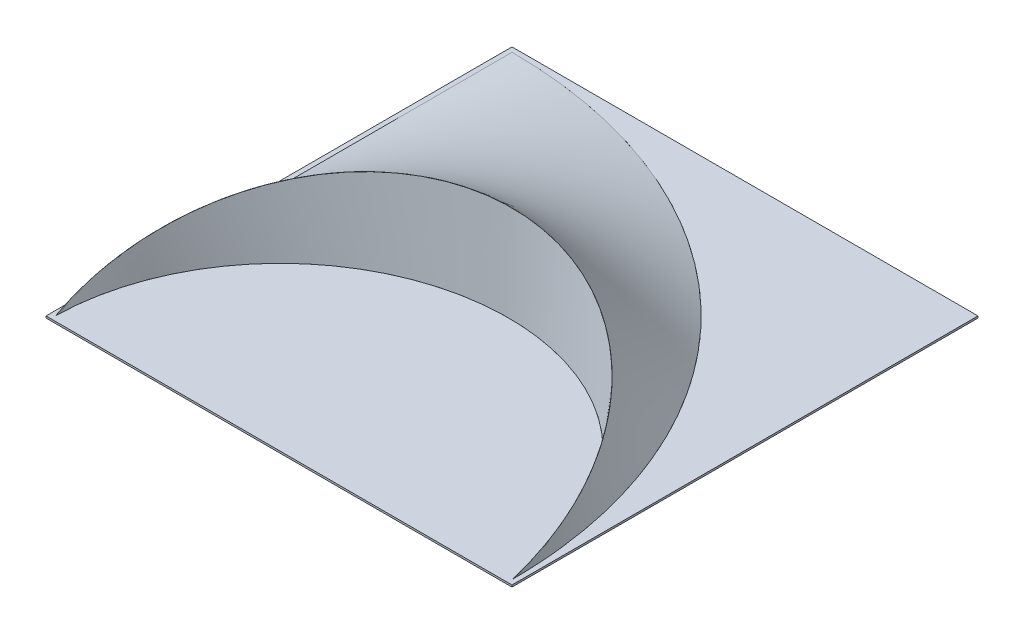
SolidWorks part; units mm, degrees
material "1060 Legierung"
ref_plane "Ebene vorne" through (0, 0, 0) normal (0, 0, 1) x (1, 0, 0)
ref_plane "Ebene oben" through (0, 0, 0) normal (0, 1, 0) x (1, 0, 0)
ref_plane "Ebene rechts" through (0, 0, 0) normal (1, 0, 0) x (0, 0, -1)
sketch "Skizze1" plane through (0, 0, 0) normal (0, 1, 0) x (1, 0, 0)
  line L0 (-244, 244) -> (244, 244) construction
  line L1 (-249, 249) -> (249, 249)
  line L2 (-249, 249) -> (-249, -249)
  line L3 (-249, -249) -> (249, -249)
  line L4 (249, 249) -> (249, -249)
  line L5 (-249, 249) -> (249, -249) construction
  line L6 (-249, -249) -> (249, 249) construction
  line L7 (244, 244) -> (244, -244) construction
  line L8 (-244, -244) -> (244, -244) construction
  line L9 (-244, 244) -> (-244, -244) construction
  line L10 (0, 249) -> (0, -249) construction
  arc A0 (-244, 244) -> (244, -244) centre (-244, -244) cw construction
  arc A1 (-244, -244) -> (244, -244) centre (0, -244) cw construction
  point P0 (0, 0)
  dimension "D1" = 498
  dimension "D2" = 498
  dimension "D3" = 5
extrude "Aufsatz-Linear austragen1" add sketch "Skizze1" against normal blind 2 contours L2 L3 L4 L1
sketch3d "3D-Skizze1"
  line L0 (0, 0, 0) -> (0, 100, 0) construction
  line L2 (0, 100, 0) -> (0, 0, 5.2408) construction
  line L8 (-244, 0, 244) -> (-244, 0, -244)
  line L16 (0, 0, -249) -> (0, 0, 249) construction
  arc A0 (-244, 0, 244) -> (244, 0, 244) centre (0, 7.1905, 226.4551) cw
  arc A1 (244, 0, 244) -> (-244, 0, -244) centre (-244, 0, 244) cw
  arc A4 (-244, 0, 244) -> (244, 0, 244) centre (0, 0, 247.6965) cw construction
  point P5 (0, -219.2646, 133.6457)
  point P10 (-244, 488, 244)
  point P20 (0, -244.028, 247.6965)
  dimension "D1" = 100
  dimension "D2" = 3
surface "Oberflächenausfüllung1" sketch "3D-Skizze1"
sketch3d "3D-Skizze2"
  arc A0 (-244, 0, 244) -> (244, 0, 244) centre (0, 0, 247.6965) cw
  arc A1 (-244, 0, 244) -> (244, 0, 244) centre (0, 7.1729, 226.4959) cw
  spline S0 degree 3 poles (-243.9999, 0, 244) (-244.0404, 0.1982, 243.5162) (-244.1182, 0.5947, 242.5487) (-244.2151, 1.1344, 241.2318) (-244.3084, 1.7019, 239.8471) (-244.3925, 2.2695, 238.4622) (-244.4675, 2.8372, 237.0771) (-244.5334, 3.405, 235.6917) (-244.59, 3.9728, 234.3063) (-244.6375, 4.5407, 232.9207) (-244.6758, 5.1086, 231.535) (-244.7049, 5.6766, 230.1493) (-244.7247, 6.2445, 228.7636) (-244.7354, 6.8124, 227.378) (-244.7369, 7.3802, 225.9924) (-244.7292, 7.948, 224.6069) (-244.7123, 8.5158, 223.2215) (-244.6863, 9.0834, 221.8363) (-244.6511, 9.651, 220.4513) (-244.6067, 10.2185, 219.0666) (-244.5532, 10.7859, 217.6821) (-244.4906, 11.3531, 216.298) (-244.4189, 11.9202, 214.9142) (-244.338, 12.4872, 213.5309) (-244.2481, 13.054, 212.1479) (-244.149, 13.6206, 210.7655) (-244.0408, 14.187, 209.3835) (-243.9234, 14.7531, 208.0021) (-243.7969, 15.3191, 206.6213) (-243.6612, 15.8847, 205.2411) (-243.5163, 16.4501, 203.8616) (-243.3622, 17.0151, 202.4829) (-243.199, 17.5799, 201.1048) (-243.0267, 18.1443, 199.7276) (-242.8452, 18.7084, 198.3512) (-242.6546, 19.2721, 196.9757) (-242.4549, 19.8355, 195.6011) (-242.2461, 20.3985, 194.2275) (-242.0281, 20.961, 192.8548) (-241.801, 21.5231, 191.4832) (-241.5649, 22.0848, 190.1127) (-241.3196, 22.646, 188.7434) (-241.0652, 23.2068, 187.3752) (-240.8017, 23.767, 186.0082) (-240.5292, 24.3267, 184.6425) (-240.2475, 24.8859, 183.2781) (-239.9567, 25.4446, 181.9151) (-239.6569, 26.0026, 180.5535) (-239.3479, 26.5601, 179.1933) (-239.0299, 27.117, 177.8346) (-238.7028, 27.6732, 176.4775) (-238.3666, 28.2287, 175.1219) (-238.0213, 28.7836, 173.768) (-237.667, 29.3378, 172.4158) (-237.3036, 29.8913, 171.0653) (-236.9311, 30.4441, 169.7165) (-236.5496, 30.9961, 168.3696) (-236.1591, 31.5473, 167.0246) (-235.7595, 32.0978, 165.6815) (-235.3509, 32.6474, 164.3404) (-234.9332, 33.1962, 163.0013) (-234.5066, 33.7441, 161.6643) (-234.0709, 34.2912, 160.3294) (-233.6263, 34.8374, 158.9967) (-233.1727, 35.3827, 157.6662) (-232.7102, 35.927, 156.338) (-232.2387, 36.4704, 155.0121) (-231.7582, 37.0128, 153.6886) (-231.2689, 37.5543, 152.3675) (-230.7706, 38.0947, 151.049) (-230.2635, 38.6341, 149.7329) (-229.7474, 39.1724, 148.4195) (-229.2225, 39.7096, 147.1088) (-228.6887, 40.2457, 145.8007) (-228.1461, 40.7806, 144.4955) (-227.5946, 41.3144, 143.1931) (-227.0343, 41.847, 141.8935) (-226.4653, 42.3784, 140.597) (-225.8874, 42.9085, 139.3035) (-225.3009, 43.4374, 138.013) (-224.7056, 43.965, 136.7257) (-224.1016, 44.4913, 135.4416) (-223.4889, 45.0162, 134.1608) (-222.8676, 45.5397, 132.8833) (-222.2376, 46.0619, 131.6092) (-221.5991, 46.5827, 130.3385) (-220.952, 47.102, 129.0714) (-220.2963, 47.6198, 127.8079) (-219.6322, 48.1361, 126.548) (-218.9596, 48.6509, 125.2919) (-218.2785, 49.1642, 124.0395) (-217.5891, 49.6759, 122.791) (-216.8912, 50.186, 121.5464) (-216.1851, 50.6944, 120.3057) (-215.4706, 51.2012, 119.0691) (-214.7479, 51.7063, 117.8367) (-214.0169, 52.2097, 116.6084) (-213.2778, 52.7114, 115.3843) (-212.5305, 53.2113, 114.1646) (-211.7751, 53.7094, 112.9492) (-211.0117, 54.2056, 111.7383) (-210.2402, 54.7001, 110.5319) (-209.4608, 55.1926, 109.33) (-208.6734, 55.6833, 108.1328) (-207.8782, 56.172, 106.9403) (-207.0751, 56.6588, 105.7526) (-206.2642, 57.1436, 104.5696) (-205.4456, 57.6264, 103.3916) (-200.7801, 60.341, 96.768) (-191.6673, 65.1118, 85.1273) (-176.9244, 71.5003, 69.5392) (-160.9639, 77.2649, 55.4736) (-144.0861, 82.3551, 43.0534) (-127.0203, 86.6408, 32.5966) (-110.047, 90.1876, 23.9421) (-91.0579, 93.4715, 15.9296) (-69.2865, 96.377, 8.8402) (-44.4747, 98.6253, 3.3543) (-18.2587, 99.9296, 0.1717) (9.3419, 100.143, -0.3487) (38.0208, 99.0935, 2.2118) (66.5857, 96.7309, 7.9769) (91.4366, 93.4523, 15.9764) (112.4844, 89.733, 25.0515) (129.9382, 85.9618, 34.2531) (146.554, 81.6503, 44.7732) (165.2794, 75.8811, 58.8501) (185.1504, 68.2914, 77.369) (204.7065, 58.5464, 101.1469) (220.8436, 47.8218, 127.3148) (233.2473, 36.2203, 155.6222) (238.9815, 27.685, 176.4486) (241.2798, 22.7467, 188.4981) (241.7772, 21.5936, 191.3117) (242.2374, 20.435, 194.1385) (242.6602, 19.2711, 196.9784) (243.0451, 18.1019, 199.8313) (243.3918, 16.9275, 202.697) (243.6999, 15.7479, 205.5751) (243.9691, 14.5633, 208.4654) (244.1988, 13.3738, 211.3678) (244.3887, 12.1795, 214.282) (244.5383, 10.9804, 217.2077) (244.6473, 9.7768, 220.1446) (244.7154, 8.5687, 223.0923) (244.7422, 7.3563, 226.0506) (244.7272, 6.1398, 229.0191) (244.6697, 4.9191, 231.9975) (244.5694, 3.6944, 234.9857) (244.4249, 2.4658, 237.9833) (244.2637, 1.3779, 240.6377) (244.0938, 0.4602, 242.8771) (244.0002, 0, 243.9998) knots 0 0 0 0 0.00186 0.003719 0.005578 0.007437 0.009295 0.011153 0.013011 0.014869 0.016726 0.018583 0.02044 0.022297 0.024153 0.02601 0.027866 0.029723 0.031579 0.033435 0.035292 0.037148 0.039004 0.040861 0.042717 0.044573 0.04643 0.048287 0.050144 0.052001 0.053858 0.055715 0.057573 0.059431 0.061289 0.063147 0.065005 0.066864 0.068723 0.070582 0.072442 0.074302 0.076162 0.078023 0.079884 0.081745 0.083607 0.085469 0.087331 0.089194 0.091057 0.092921 0.094785 0.096649 0.098514 0.100379 0.102245 0.104111 0.105978 0.107845 0.109713 0.111581 0.113449 0.115318 0.117187 0.119057 0.120928 0.122798 0.12467 0.126541 0.128414 0.130286 0.132159 0.134033 0.135907 0.137781 0.139656 0.141531 0.143407 0.145282 0.147159 0.149035 0.150912 0.152789 0.154667 0.156544 0.158422 0.1603 0.162179 0.164057 0.165936 0.167815 0.169693 0.171572 0.173451 0.17533 0.177209 0.179088 0.180967 0.182845 0.184724 0.186602 0.18848 0.190358 0.192236 0.194113 0.19599 0.197867 0.199743 0.227773 0.255552 0.282902 0.309645 0.335662 0.358943 0.38166 0.413225 0.44463 0.476382 0.511398 0.547085 0.583305 0.619893 0.644704 0.66959 0.694528 0.719507 0.759241 0.799113 0.839284 0.879995 0.921553 0.925363 0.929183 0.933013 0.936855 0.940707 0.94457 0.948446 0.952333 0.956232 0.960144 0.964069 0.968006 0.971957 0.975921 0.979898 0.98389 0.987895 0.991916 0.995951 1 1 1 1 construction
  point P2 (0, -244.028, 247.6965)
  point P8 (0, -219.2833, 133.698)
surface "Oberflächenausfüllung2" sketch "3D-Skizze2"
sketch "Skizze3" plane through (0, -2, 0) normal (0, -1, 0) x (1, 0, 0)
  line L0 (-244, 244) -> (-244, -244) construction
  line L1 (-244, 244) -> (-244, -244)
  line L4 (-249, -249) -> (249, -249)
  line L5 (249, -249) -> (249, 249)
  line L6 (249, 249) -> (-249, 249)
  line L7 (-249, 249) -> (-249, -249)
  line L8 (-249, -249) -> (249, -249)
  line L9 (249, -249) -> (249, 249)
  line L10 (249, 249) -> (-249, 249)
  line L11 (-249, 249) -> (-249, -249)
  arc A0 (-244, -244) -> (244, 244) centre (-244, 244) ccw construction
  arc A1 (-244, 244) -> (244, 244) centre (0, 247.6965) ccw construction
  arc A2 (-244, -244) -> (244, 244) centre (-244, 244) ccw
  arc A3 (-244, 244) -> (244, 244) centre (0, 247.6965) ccw
  dimension "D1" = 0
extrude "Schnitt-Linear austragen2" cut sketch "Skizze3" against normal up to surface (2 mm away) contours A3 L1 A2 up to face at (0, 0, 0)
